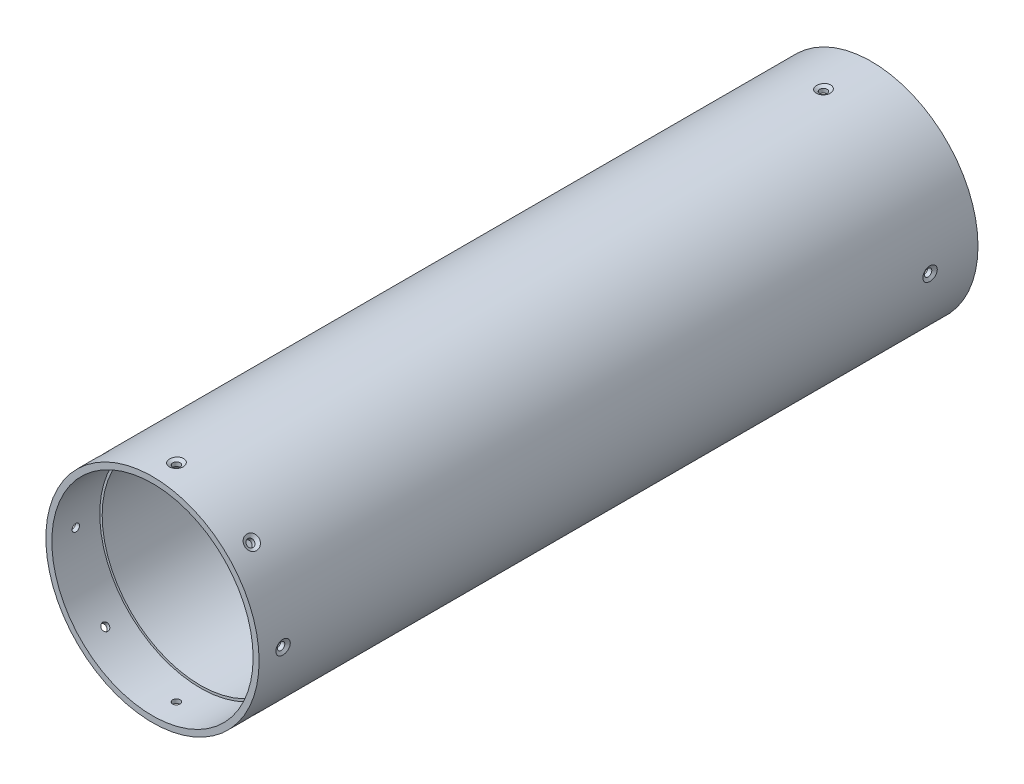
SolidWorks part; units mm, degrees
material "Hexcel AS4C (3000 Filaments)"
ref_plane "Plan de face" through (0, 0, 0) normal (0, 0, 1) x (1, 0, 0)
ref_plane "Plan de dessus" through (0, 0, 0) normal (0, 1, 0) x (1, 0, 0)
ref_plane "Plan de droite" through (0, 0, 0) normal (1, 0, 0) x (0, 0, -1)
sketch "Esquisse1" plane through (0, 0, 0) normal (0, 0, 1) x (1, 0, 0)
  circle A0 centre (0, 0) radius 42
  circle A1 centre (0, 0) radius 44.5
  dimension "D1" = 89
  dimension "D2" = 84
extrude "Boss.-Extru.1" add sketch "Esquisse1" along normal blind 300
hole_wizard "Dégagement M31" positions "Esquisse3D1" profile "Esquisse2" hole size "M3" standard "ISO"
sketch3d "Esquisse3D1"
  line L0 (0, 0, 0) -> (0, 0, 424.0623) construction
  line L4 (0, 0, 0) -> (-77.0322, 0, 0) construction
  line L6 (-44.5, 0, 0) -> (-44.5, 0, 353.7245) construction
  circle A0 centre (0, 0, 0) radius 44.5 construction
  point P0 (-44.5, 0, 20)
  point P17 (0, 0, 44.5)
  point P22 (0, 0, 292.3054)
  dimension "D1" = 20
sketch "Esquisse2" plane through (-44.5, 0, 20) normal (0, 1, 0) x (0, 0, 1)
  line L0 (0, 0) -> (0, 89)
  line L1 (0, 89) -> (1.55, 89)
  line L2 (1.55, 89) -> (1.55, 0.8372)
  line L3 (1.55, 0.8372) -> (3, 0)
  line L5 (3, 0) -> (0, 0)
  line L6 (-1.55, 0.8372) -> (-3, 0) construction
  line L11 (0, -6.35) -> (0, 107.95) construction
  dimension "Diamètre du perçage jusqu'au prochain" = 3.1
  dimension "Profondeur du perçage jusqu'au prochain" = 89
  dimension "Diamètre du fraisage entrant" = 6
  dimension "Angle du fraisage entrant" = 120
pattern_circular "Répétition circulaire1" count 4 over 360 about axis through (0, 0, 0) along (0, 0, 1) of "Dégagement M31"
hole_wizard "Dégagement M2.52" positions "Esquisse3D3" profile "Esquisse4" hole size "M2.5" standard "ISO" end condition through all
sketch3d "Esquisse3D3"
  line L1 (0, 0, 300) -> (-63.7663, 0, 300) construction
  line L4 (-44.5, 0, 258.6894) -> (-44.5, 0, 300) construction
  circle A0 centre (0, 0, 300) radius 42 construction
  point P0 (-44.5, 0, 290)
  point P27 (0, 0, 342)
  dimension "D1" = 10
sketch "Esquisse4" plane through (-44.5, 0, 290) normal (0, 1, 0) x (0, 0, 1)
  line L0 (0, 0) -> (0, 107.4325)
  line L1 (0, 107.4325) -> (1.55, 107.4325)
  line L2 (1.55, 107.4325) -> (1.55, 0.8372)
  line L3 (1.55, 0.8372) -> (3, 0)
  line L5 (3, 0) -> (0, 0)
  line L6 (-1.55, 0.8372) -> (-3, 0) construction
  line L11 (0, -6.35) -> (0, 107.95) construction
  dimension "Diamètre du perçage jusqu'au prochain" = 3.1
  dimension "Profondeur du perçage jusqu'au prochain" = 107.4325
  dimension "Diamètre du fraisage entrant" = 6
  dimension "Angle du fraisage entrant" = 120
pattern_circular "Répétition circulaire2" count 8 over 360 about axis through (0, 0, 300) along (0, 0, 1) of "Dégagement M2.52"
sketch "Esquisse5" plane through (0, 0, 0) normal (0, 1, 0) x (1, 0, 0)
  line L0 (0, -328.7499) -> (0, 36.4498) construction
  line L1 (0, -280) -> (100.5989, -280) construction
  line L2 (0, -300) -> (44.5, -300) construction
  line L5 (42, -280) -> (42, -300) construction
  line L8 (42, -280) -> (41, -280)
  line L9 (41, -280) -> (41, -27)
  line L10 (0, -27) -> (61.3801, -27) construction
  line L11 (0, 0) -> (42, 0) construction
  line L14 (42, -27) -> (42, 0) construction
  line L17 (42, -27) -> (42, -280)
  line L18 (41, -27) -> (42, -27)
  point P11 (22.25, -300)
  dimension "D1" = 20
  dimension "D2" = 27
  dimension "D3" = 1
revolve "Révolution1" add sketch "Esquisse5" angle 360 about L0
